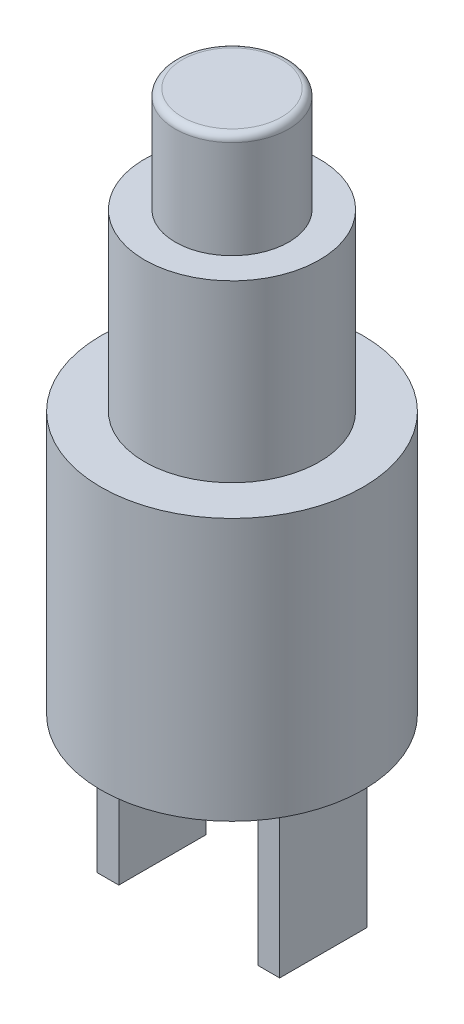
SolidWorks part; units mm, degrees
ref_plane "Front Plane" through (0, 0, 0) normal (0, 0, 1) x (1, 0, 0)
ref_plane "Top Plane" through (0, 0, 0) normal (0, 1, 0) x (1, 0, 0)
ref_plane "Right Plane" through (0, 0, 0) normal (1, 0, 0) x (0, 0, -1)
sketch "Sketch1" plane through (0, 0, 0) normal (0, 1, 0) x (1, 0, 0)
  circle A0 centre (0, 0) radius 4.7625
  dimension "D1" = 9.525
extrude "Boss-Extrude1" add sketch "Sketch1" against normal blind 9.525
sketch "Sketch2" plane through (0, 0, 0) normal (0, 1, 0) x (1, 0, 0)
  circle A0 centre (0, 0) radius 3.175
  dimension "D1" = 6.35
extrude "Boss-Extrude2" add sketch "Sketch2" along normal blind 6.35
cosmetic thread "Cosmetic Thread1" parameters "D2"=5.268
sketch "Sketch3" plane through (0, 6.35, 0) normal (0, 1, 0) x (1, 0, 0)
  circle A0 centre (0, 0) radius 2.0574
  dimension "D1" = 4.1148
extrude "Boss-Extrude3" add sketch "Sketch3" along normal blind 3.81
sketch "Sketch4" plane through (0, -9.525, 0) normal (0, -1, 0) x (1, 0, 0)
  line L0 (0, 0) -> (2.921, 0) construction
  line L1 (0, 0) -> (0, 4.7625) construction
  line L2 (3.3179, -1.5875) -> (2.5241, -1.5875)
  line L3 (3.3179, -1.5875) -> (3.3179, 1.5875)
  line L4 (3.3179, 1.5875) -> (2.5241, 1.5875)
  line L5 (2.5241, -1.5875) -> (2.5241, 1.5875)
  line L6 (3.3179, -1.5875) -> (2.5241, 1.5875) construction
  line L7 (3.3179, 1.5875) -> (2.5241, -1.5875) construction
  line L8 (-3.3179, 1.5875) -> (-2.5241, 1.5875)
  line L9 (-2.5241, -1.5875) -> (-2.5241, 1.5875)
  line L10 (-3.3179, -1.5875) -> (-2.5241, -1.5875)
  line L11 (-3.3179, -1.5875) -> (-3.3179, 1.5875)
  circle A0 centre (0, 0) radius 4.7625 construction
  dimension "D1" = 3.175
  dimension "D2" = 0.7937
  dimension "D3" = 2.921
extrude "Boss-Extrude4" add sketch "Sketch4" along normal blind 5.842
fillet "Fillet1" radius 0.254 1 edges at (0, 10.16, 2.0574)
sketch "Sketch5" plane through (0, 0, 0) normal (0, 1, 0) x (1, 0, 0)
  line L1 (-2.7496, -4.7625) -> (2.7496, -4.7625)
  line L2 (2.7496, -4.7625) -> (5.4993, 0)
  line L3 (5.4993, 0) -> (2.7496, 4.7625)
  line L4 (2.7496, 4.7625) -> (-2.7496, 4.7625)
  line L5 (-2.7496, 4.7625) -> (-5.4993, 0)
  line L6 (-5.4993, 0) -> (-2.7496, -4.7625)
  circle A0 centre (0, 0) radius 4.7625 construction
  circle A1 centre (0, 0) radius 3.175
  circle A2 centre (0, 0) radius 3.175 construction
  dimension "D1" = 9.525
extrude "Boss-Extrude5" [suppressed] add sketch "Sketch5" along normal blind 2.7686 separate body
